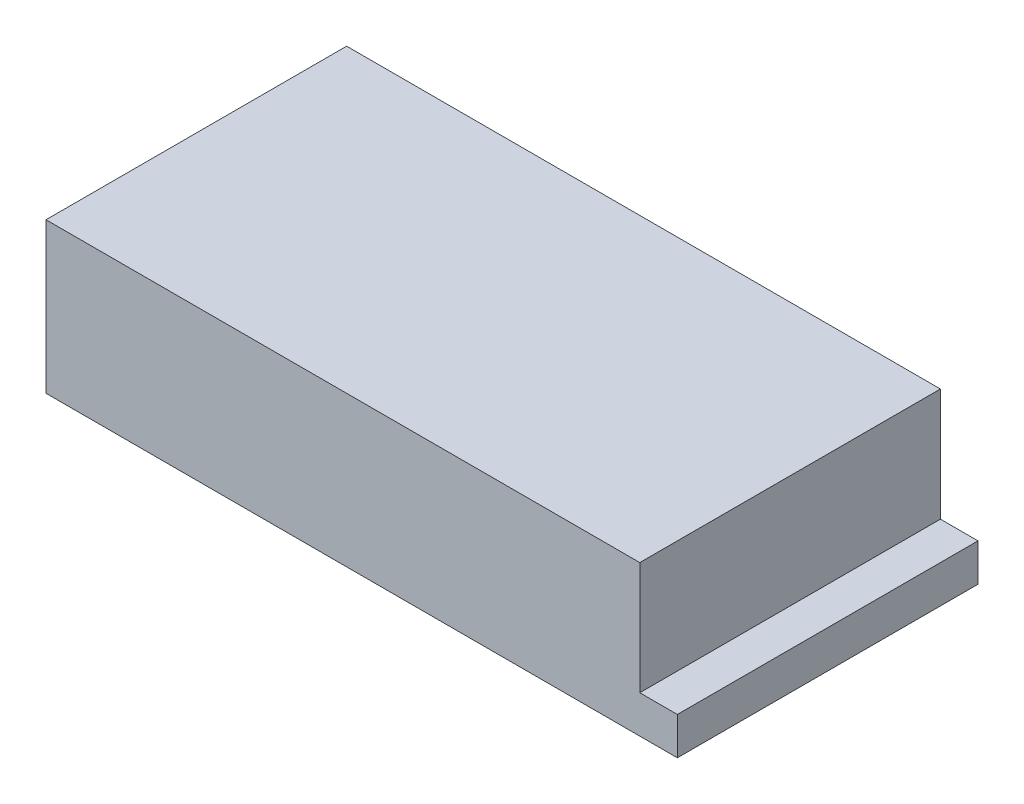
SolidWorks part; units mm, degrees
ref_plane "前视基准面" through (0, 0, 0) normal (0, 0, 1) x (1, 0, 0)
ref_plane "上视基准面" through (0, 0, 0) normal (0, 1, 0) x (1, 0, 0)
ref_plane "右视基准面" through (0, 0, 0) normal (1, 0, 0) x (0, 0, -1)
sketch "草图1" plane through (0, 0, 0) normal (0, 0, 1) x (1, 0, 0)
  line L0 (-48.3825, 0) -> (119.6175, 0)
  line L1 (119.6175, 0) -> (119.6175, 10)
  line L2 (119.6175, 10) -> (109.6175, 10)
  line L3 (109.6175, 10) -> (109.6175, 40)
  line L4 (109.6175, 40) -> (-48.3825, 40)
  line L5 (-48.3825, 40) -> (-48.3825, 0)
extrude "凸台-拉伸1" add sketch "草图1" along normal blind 80
